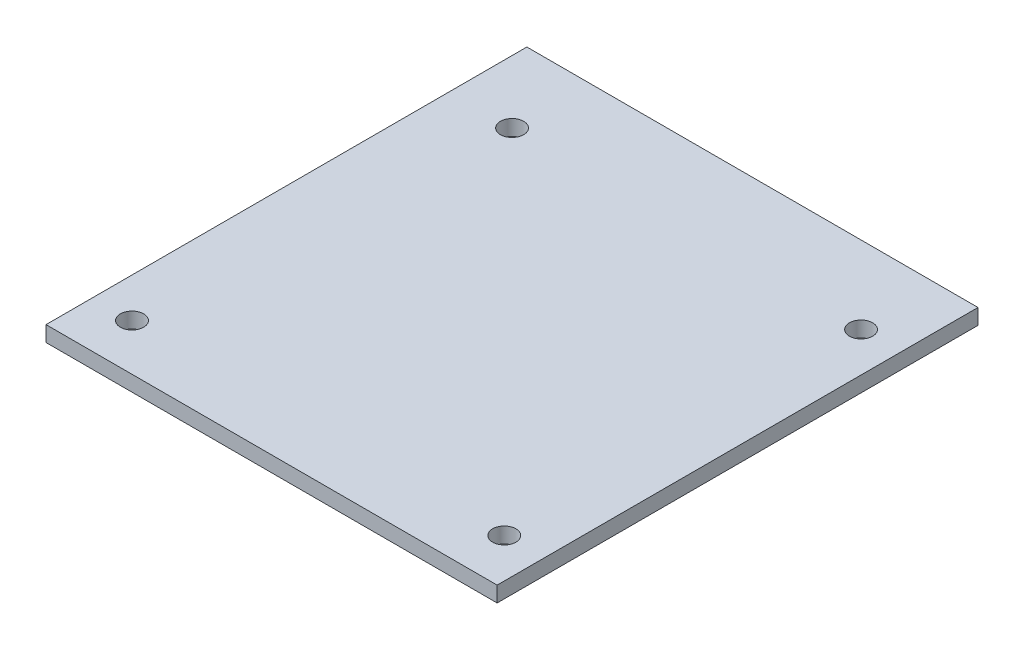
SolidWorks part; units mm, degrees
ref_plane "Front Plane" through (0, 0, 0) normal (0, 0, 1) x (1, 0, 0)
ref_plane "Top Plane" through (0, 0, 0) normal (0, 1, 0) x (1, 0, 0)
ref_plane "Right Plane" through (0, 0, 0) normal (1, 0, 0) x (0, 0, -1)
sketch "Sketch1" plane through (0, 0, 0) normal (0, 1, 0) x (1, 0, 0)
  line L0 (-37.7535, -25) -> (39.7749, -25) construction
  line L1 (-29.085, -31) -> (29.085, -31)
  line L2 (-29.085, -31) -> (-29.085, 31)
  line L3 (-29.085, 31) -> (29.085, 31)
  line L4 (29.085, -31) -> (29.085, 31)
  line L5 (-29.085, -31) -> (29.085, 31) construction
  line L6 (-29.085, 31) -> (29.085, -31) construction
  line L7 (24.005, -25) -> (24.005, 43.1608) construction
  line L8 (24.005, 21) -> (-35.4155, 21) construction
  circle A0 centre (24.005, -25) radius 1.5
  circle A1 centre (-23.995, -25) radius 1.5
  circle A2 centre (24.005, 21) radius 1.5
  circle A3 centre (-20.995, 21) radius 1.5
  point P0 (0, 0)
  dimension "D4" = 3
  dimension "D6" = 3
  dimension "D9" = 3
  dimension "D10" = 3
  dimension "D1" = 58.17
  dimension "D2" = 62
  dimension "D3" = 6
  dimension "D5" = 5.08
  dimension "D7" = 48
  dimension "D8" = 46
  dimension "D11" = 45
extrude "Boss-Extrude1" add sketch "Sketch1" along normal blind 2
